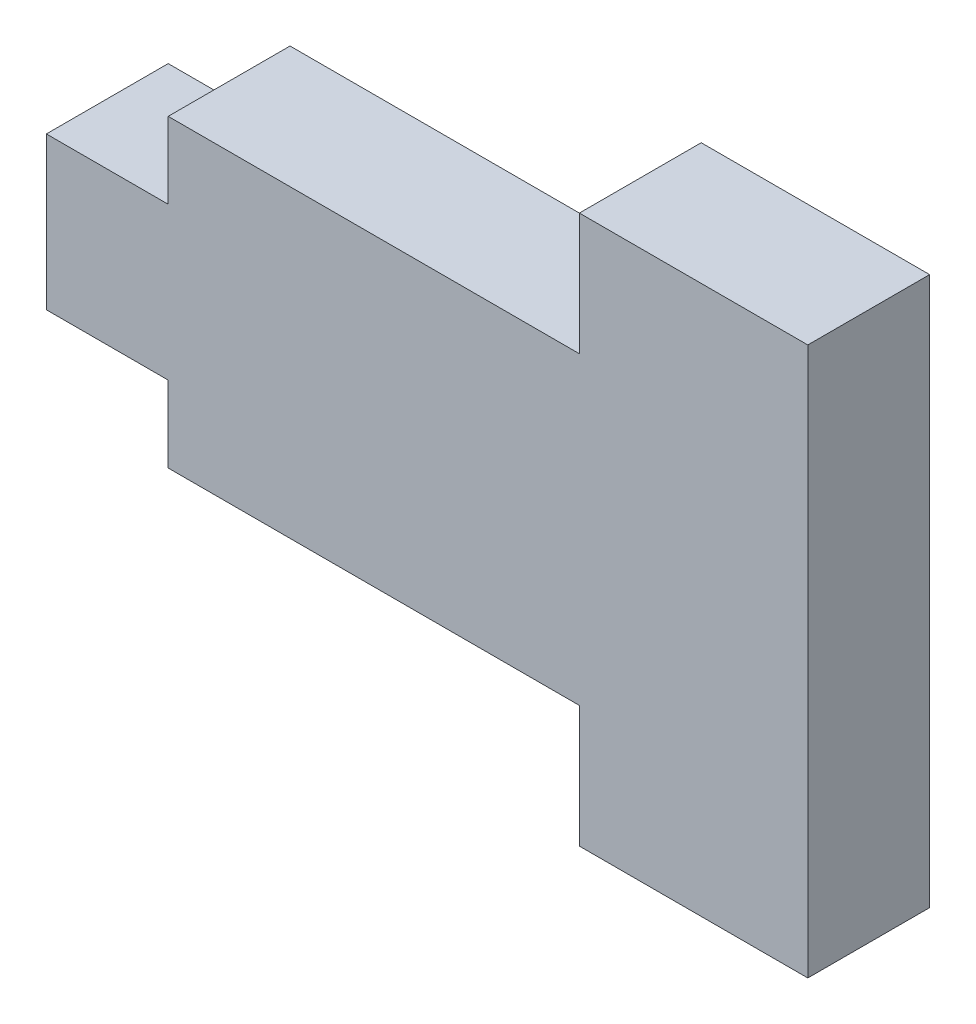
SolidWorks part; units mm, degrees
ref_plane "Front" through (0, 0, 0) normal (0, 0, 1) x (1, 0, 0)
ref_plane "Top" through (0, 0, 0) normal (0, 1, 0) x (1, 0, 0)
ref_plane "Right" through (0, 0, 0) normal (1, 0, 0) x (0, 0, -1)
sketch "Sketch1" plane through (0, 0, 0) normal (0, 0, 1) x (1, 0, 0)
  line L1 (-13.335, 6.35) -> (13.335, 6.35)
  line L2 (-13.335, 6.35) -> (-13.335, -6.35)
  line L3 (-13.335, -6.35) -> (13.335, -6.35)
  line L4 (13.335, 6.35) -> (13.335, -6.35)
  line L5 (-13.335, 6.35) -> (13.335, -6.35) construction
  line L6 (-13.335, -6.35) -> (13.335, 6.35) construction
  line L7 (13.335, 6.35) -> (3.81, 6.35)
  line L8 (13.335, 6.35) -> (13.335, 11.43)
  line L9 (13.335, 11.43) -> (3.81, 11.43)
  line L10 (3.81, 6.35) -> (3.81, 11.43)
  line L11 (13.335, -6.35) -> (3.81, -6.35)
  line L12 (13.335, -6.35) -> (13.335, -11.43)
  line L13 (13.335, -11.43) -> (3.81, -11.43)
  line L14 (3.81, -6.35) -> (3.81, -11.43)
  line L15 (-18.415, 3.175) -> (-13.335, 3.175)
  line L16 (-18.415, 3.175) -> (-18.415, -3.175)
  line L17 (-18.415, -3.175) -> (-13.335, -3.175)
  line L18 (-13.335, 3.175) -> (-13.335, -3.175)
  line L19 (-18.415, 3.175) -> (-13.335, -3.175) construction
  line L20 (-18.415, -3.175) -> (-13.335, 3.175) construction
  point P0 (0, 0)
  point P12 (-15.875, 0)
  point P17 (0, 0)
  dimension "D1" = 12.7
  dimension "D2" = 26.67
  dimension "D3" = 9.525
  dimension "D4" = 5.08
  dimension "D5" = 6.35
extrude "Boss-Extrude1" add sketch "Sketch1" along normal blind 5.08 contours L16 L17 L2 L15 | L4 L1 L2 L3 | L10 L1 L8 L9 | L3 L14 L13 L12
